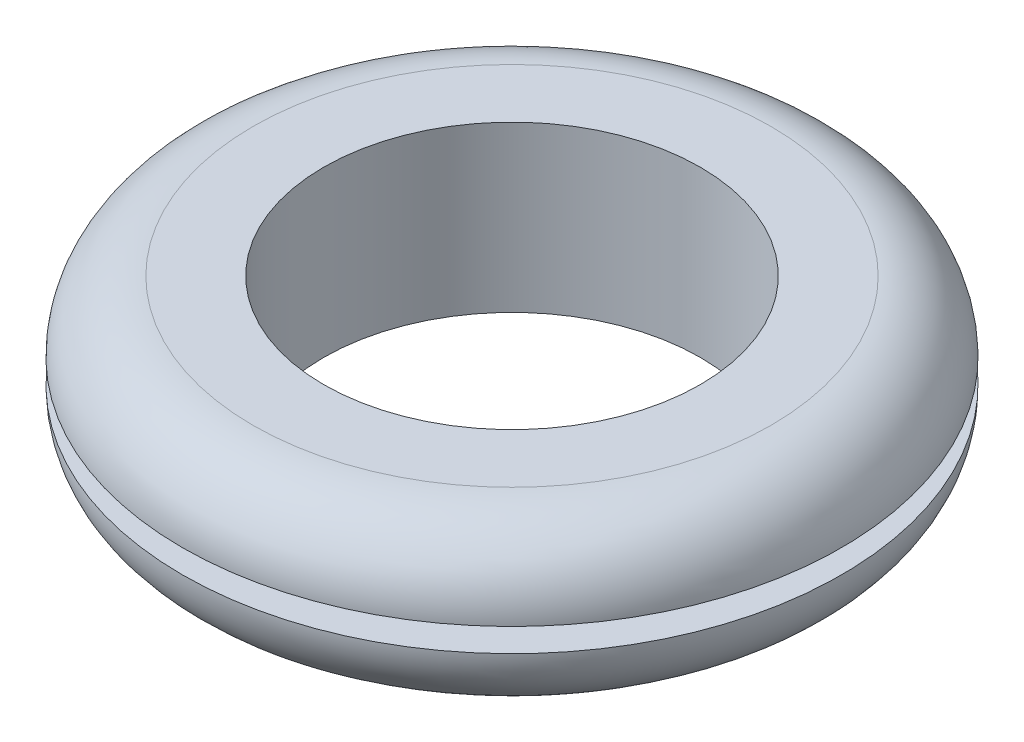
SolidWorks part; units mm, degrees
ref_plane "Front" through (0, 0, 0) normal (0, 0, 1) x (1, 0, 0)
ref_plane "Top" through (0, 0, 0) normal (0, 1, 0) x (1, 0, 0)
ref_plane "Right" through (0, 0, 0) normal (1, 0, 0) x (0, 0, -1)
sketch "Sketch1" plane through (0, 0, 0) normal (1, 0, 0) x (0, 0, -1)
  line L0 (0, -5.5562) -> (0, 5.5562) construction
  line L1 (0, 0.7937) -> (0, -0.7937) construction
  line L2 (-22.225, 5.5562) -> (22.225, 5.5563) construction
  line L3 (-12.7, 0.7937) -> (12.7, 0.7938) construction
  line L4 (-17.4625, 0) -> (17.4625, 0) construction
  point P12 (-12.7, 0.7937)
  point P13 (12.7, 0.7938)
  point P14 (-17.4625, 0)
  point P15 (17.4625, 0)
  point P16 (-22.225, 5.5562)
  point P17 (0, -5.5562)
  point P18 (22.225, 5.5563)
  point P19 (0, 5.5562)
  point P20 (0, 0.7937)
  point P21 (0, -0.7937)
  dimension "Overall Height E" = 11.1125
  dimension "Material Thickness B" = 1.5875
  dimension "Flange Diameter D" = 44.45
  dimension "ID C" = 25.4
  dimension "For ID A" = 34.925
sketch "Sketch2" plane through (0, 0, 0) normal (1, 0, 0) x (0, 0, -1)
  line L0 (-12.7, -5.5562) -> (-12.7, 5.5562)
  line L1 (-12.7, 5.5562) -> (-17.4625, 5.5563)
  line L2 (-17.4625, 0.7938) -> (-17.4625, -0.7938)
  line L3 (-17.4625, 0.7938) -> (-22.225, 0.7938)
  line L4 (-17.4625, -0.7938) -> (-22.225, -0.7938)
  line L5 (-12.7, -5.5562) -> (-17.4625, -5.5563)
  arc A0 (-22.225, 0.7938) -> (-17.4625, 5.5563) centre (-17.4625, 0.7937) cw
  arc A1 (-22.225, -0.7938) -> (-17.4625, -5.5563) centre (-17.4625, -0.7937) ccw
  point P4 (-22.225, 0.7937)
revolve "Revolve1" add sketch "Sketch2" angle 360 about L0
ref_plane "Plane1" through (0, 5.5563, 0) normal (0, -1, 0) x (0, 0, -1)
sketch "Sketch3" plane through (0, 5.5563, 0) normal (0, -1, 0) x (0, 0, -1)
  line L0 (0, -22.225) -> (0, 22.225) construction
  line L1 (-22.225, 0) -> (22.225, 0) construction
  line L2 (0, 12.7) -> (0, -12.7) construction
  line L3 (-12.7, 0) -> (12.7, 0) construction
  line L4 (0, 17.4625) -> (0, -17.4625) construction
  line L5 (-17.4625, 0) -> (17.4625, 0) construction
  point P11 (0, 22.225)
  point P12 (0, 12.7)
  point P13 (0, -12.7)
  point P14 (0, -22.225)
  point P19 (0, -17.4625)
  point P20 (0, 17.4625)
